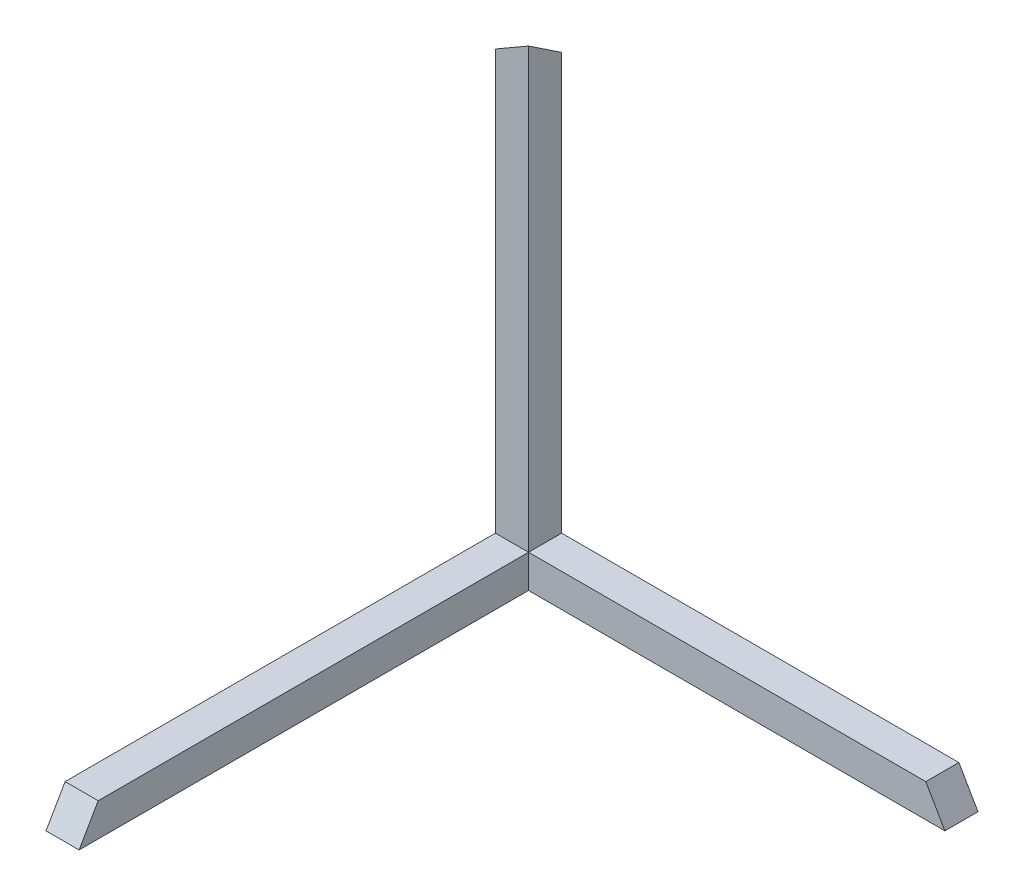
SolidWorks part; units mm, degrees
ref_plane "Front Plane" through (0, 0, 0) normal (0, 0, 1) x (1, 0, 0)
ref_plane "Top Plane" through (0, 0, 0) normal (0, 1, 0) x (1, 0, 0)
ref_plane "Right Plane" through (0, 0, 0) normal (1, 0, 0) x (0, 0, -1)
sketch "Sketch1" plane through (0, 0, 0) normal (0, 0, 1) x (1, 0, 0)
  line L1 (-77.5074, 22.3679) -> (-72.5074, 22.3679)
  line L2 (-77.5074, 22.3679) -> (-77.5074, -42.6321)
  line L3 (-77.5074, -42.6321) -> (-72.5074, -42.6321)
  line L4 (-72.5074, 22.3679) -> (-72.5074, -42.6321)
  dimension "D1" = 65
  dimension "D2" = 5
extrude "Boss-Extrude1" add sketch "Sketch1" along normal blind 5
sketch "Sketch2" plane through (-77.5074, 0, 0) normal (-1, 0, 0) x (0, 0, 1)
  line L0 (5, 22.3679) -> (5, -42.6321) construction
  line L1 (5, -42.6321) -> (70, -42.6321)
  line L2 (5, -42.6321) -> (5, -37.6321)
  line L3 (5, -37.6321) -> (70, -37.6321)
  line L4 (70, -42.6321) -> (70, -37.6321)
  point P4 (0, 0)
  point P5 (70, -37.6321)
  point P7 (5, -37.6321)
  point P8 (5, -37.6321)
  dimension "D1" = 5
  dimension "D2" = 65
sketch "Sketch3" plane through (0, 0, 5) normal (0, 0, 1) x (1, 0, 0)
extrude "Boss-Extrude3" add sketch "Sketch2" against normal blind 5 contours L3 L4 L1 L2
sketch "Sketch4" plane through (0, -37.6321, 0) normal (0, 1, 0) x (1, 0, 0)
  line L1 (-77.5074, 0) -> (-12.5074, 0)
  line L2 (-77.5074, 0) -> (-77.5074, -5)
  line L3 (-77.5074, -5) -> (-12.5074, -5)
  line L4 (-12.5074, 0) -> (-12.5074, -5)
  dimension "D1" = 5
  dimension "D2" = 65
extrude "Boss-Extrude4" add sketch "Sketch4" against normal blind 5
draft "Draft3" type of draft neutral plane draft angle 30 faces to draft 1 face at (-12.5074, -40.1321, 2.5) neutral plane through (0, -37.6321, 0) neutral plane normal (0, 1, 0) parameters "D1"=30
draft "Draft4" type of draft neutral plane draft angle 30 faces to draft 1 face at (-11.0641, -40.1321, 2.5) neutral plane through (0, -37.6321, 0) neutral plane normal (0, 1, 0) parameters "D1"=30
draft "Draft7" type of draft neutral plane draft angle 30 faces to draft 1 face at (-75.0074, -40.1321, 70) neutral plane through (-72.5074, -37.6321, 5) neutral plane normal (0, 1, 0) parameters "D1"=30
draft "Draft8" type of draft neutral plane draft angle 30 faces to draft 1 face at (-75.0074, 22.3679, 2.5) neutral plane through (-77.5074, 22.3679, 5) neutral plane normal (-1, 0, 0) parameters "D1"=30
draft "Draft9" type of draft neutral plane draft angle 30 faces to draft 1 face at (-75.0074, 23.8113, 2.5) neutral plane through (0, 0, 0) neutral plane normal (0, 0, -1) parameters "D1"=30
